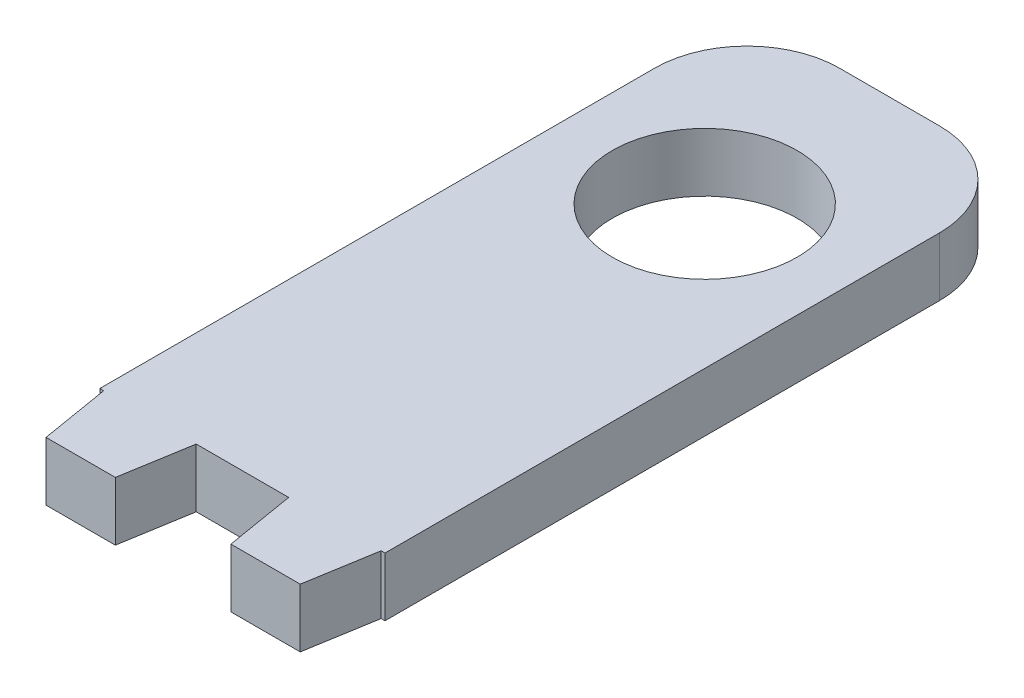
SolidWorks part; units mm, degrees
ref_plane "Front Plane" through (0, 0, 0) normal (0, 0, 1) x (1, 0, 0)
ref_plane "Top Plane" through (0, 0, 0) normal (0, 1, 0) x (1, 0, 0)
ref_plane "Right Plane" through (0, 0, 0) normal (1, 0, 0) x (0, 0, -1)
sketch "Sketch1" plane through (0, 0, 0) normal (0, 1, 0) x (1, 0, 0)
  line L0 (0, 0) -> (0, -38545.911) construction
  line L1 (-15.4184, 35) -> (15.4184, 35)
  line L2 (-15.4184, 35) -> (-15.4184, -35)
  line L3 (-15.4184, -35) -> (15.4184, -35)
  line L4 (15.4184, 35) -> (15.4184, -35)
  line L5 (-15.4184, 35) -> (15.4184, -35) construction
  line L6 (-15.4184, -35) -> (15.4184, 35) construction
  line L7 (-10, -35) -> (-10, -42.5) construction
  line L8 (-15, -35) -> (-5, -35)
  line L9 (-15, -35) -> (-13.75, -42.5)
  line L10 (-13.75, -42.5) -> (-6.25, -42.5)
  line L11 (-5, -35) -> (-6.25, -42.5)
  line L12 (10, -35) -> (10, -42.5) construction
  line L13 (5, -35) -> (6.25, -42.5)
  line L14 (13.75, -42.5) -> (6.25, -42.5)
  line L15 (15, -35) -> (13.75, -42.5)
  line L16 (15, -35) -> (5, -35)
  circle A0 centre (0, 15) radius 10
  point P0 (0, 0)
  point P13 (-10, -42.5)
  dimension "D1" = 10
  dimension "D2" = 7.5
  dimension "D3" = 7.5
  dimension "D4" = 0
  dimension "D5" = 5
  dimension "D6" = 70
  dimension "D7" = 50
extrude "Boss-Extrude1" add sketch "Sketch1" along normal blind 6.35 contours L15 L3 L13 L14 | L11 L3 L9 L10 | L4 L1 L2 L3 A0
fillet "Fillet1" radius 10 2 edges at (-15.4184, 3.175, -35) (15.4184, 3.175, -35)
equation "\"toothBaseWidth\"=0.01"
equation "\"toothEndWidth\"=0.0075"
equation "\"toothLength\"=0.0075"
equation "\"D2@Sketch1\"=\"toothEndWidth\""
equation "\"D1@Sketch1\"= \"toothBaseWidth\""
equation "\"D3@Sketch1\"=\"toothLength\""
equation "\"holeWidth\" = 0.009"
equation "\"motorHolderToothSeparation\" = 0.01"
equation "\"magnetHolderToothSeparation\" = 0.02"
equation "\"D5@Sketch1\"= \"motorHolderToothSeparation\"/2"
